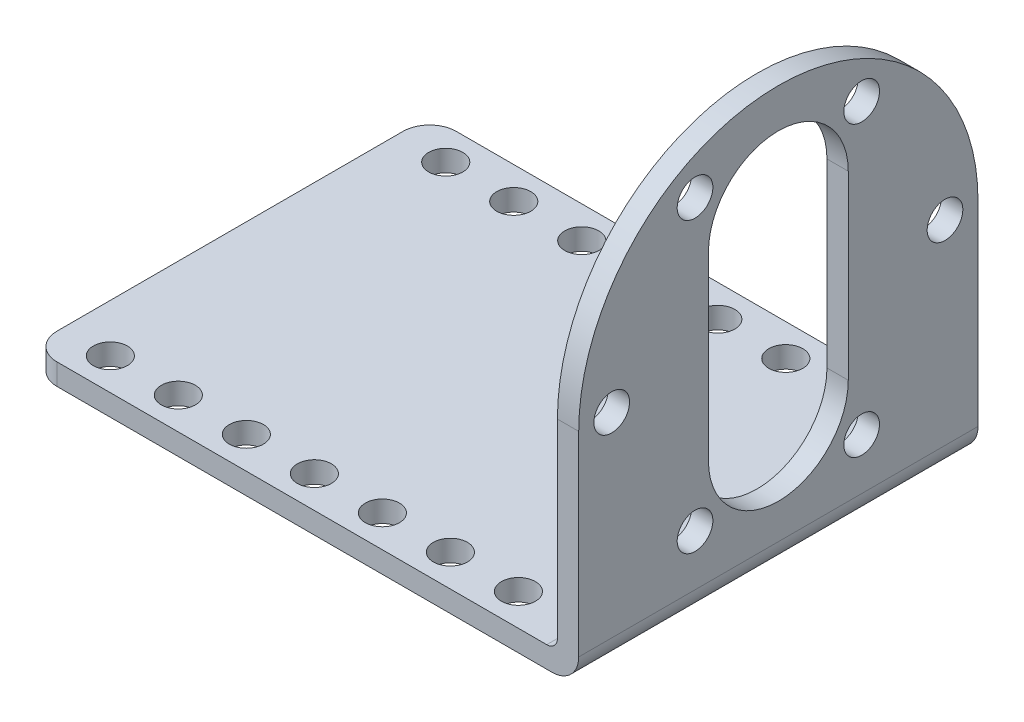
SolidWorks part; units mm, degrees
material "1060 Alloy"
ref_plane "Front Plane" through (0, 0, 0) normal (0, 0, 1) x (1, 0, 0)
ref_plane "Top Plane" through (0, 0, 0) normal (0, 1, 0) x (1, 0, 0)
ref_plane "Right Plane" through (0, 0, 0) normal (1, 0, 0) x (0, 0, -1)
sketch "Sketch1" plane through (0, 0, 0) normal (1, 0, 0) x (0, 0, -1)
  line L0 (-766.126, 0) -> (37540.1761, 0) construction
  line L1 (0, -766.126) -> (0, 37540.1761) construction
  line L2 (18.75, 0) -> (-18.75, 0)
  line L3 (-18.75, 0) -> (-18.75, 39.6)
  line L4 (18.75, 0) -> (18.75, 39.6)
  line L5 (-1000, 20.85) -> (49000, 20.85) construction
  line L6 (-6.565, 29.35) -> (-6.565, 12.35)
  line L7 (6.565, 29.35) -> (6.565, 12.35)
  arc A0 (18.75, 20.85) -> (-18.75, 20.85) centre (0, 20.85) ccw
  circle A1 centre (0, 20.85) radius 15.65 construction
  circle A2 centre (-15.65, 20.85) radius 1.675
  circle A3 centre (-7.825, 34.4033) radius 1.675
  circle A4 centre (7.825, 34.4033) radius 1.675
  circle A5 centre (15.65, 20.85) radius 1.675
  circle A6 centre (7.825, 7.2967) radius 1.675
  circle A7 centre (-7.825, 7.2967) radius 1.675
  circle A8 centre (0, 29.35) radius 6.565
  circle A10 centre (0, 12.35) radius 6.565
  point P18 (0, 0)
  point P31 (0, 20.85)
  dimension "D4" = 31.3
  dimension "D5" = 3.35
  dimension "D7" = 13.13
  dimension "D1" = 18.75
  dimension "D2" = 39.6
  dimension "D3" = 20.85
  dimension "D8" = 8.5
  dimension "D6" = 6
extrude "Boss-Extrude1" add sketch "Sketch1" along normal blind 2 contours L4 A0 L3 L2 A7 A6 A5 A4 A3 A2 L7 A10 L6 A8
sketch "Sketch2" plane through (0, 0, 0) normal (0, 1, 0) x (1, 0, 0)
  line L0 (-1000, 0) -> (49000, 0) construction
  line L1 (0, -18.75) -> (0, 18.75)
  line L2 (0, 18.75) -> (-49.5, 18.75)
  line L3 (-49.5, 18.75) -> (-49.5, -18.75)
  line L4 (0, -18.75) -> (-49.5, -18.75)
  line L5 (2, -18.75) -> (2, 18.75) construction
  circle A0 centre (-44.9875, 15.75) radius 1.6
  circle A1 centre (-38.6, 15.75) radius 1.6
  circle A2 centre (-32.2125, 15.75) radius 1.6
  circle A3 centre (-25.825, 15.75) radius 1.6
  circle A4 centre (-19.4375, 15.75) radius 1.6
  circle A5 centre (-13.05, 15.75) radius 1.6
  circle A6 centre (-6.6625, 15.75) radius 1.6
  circle A7 centre (-6.6625, -15.75) radius 1.6
  circle A8 centre (-13.05, -15.75) radius 1.6
  circle A9 centre (-19.4375, -15.75) radius 1.6
  circle A10 centre (-44.9875, -15.75) radius 1.6
  circle A11 centre (-38.6, -15.75) radius 1.6
  circle A12 centre (-32.2125, -15.75) radius 1.6
  circle A13 centre (-25.825, -15.75) radius 1.6
  point P9 (0, 0)
  point P10 (-49.5, 0)
  point P39 (0, 0)
  point P40 (0, 0)
  point P41 (0, 0)
  point P42 (0, 0)
  point P43 (0, 0)
  dimension "D2" = 3.2
  dimension "D1" = 49.5
  dimension "D3" = 15.05
  dimension "D4" = 15.75
  dimension "D6" = 25.55
  dimension "D5" = 7
extrude "Boss-Extrude2" add sketch "Sketch2" along normal blind 2
fillet "Fillet1" radius 2.5 3 edges at (2, 0, 0) (-49.5, 1, -18.75) (-49.5, 1, 18.75)
fillet "Fillet2" radius 1 1 edges at (0, 2, 0)
